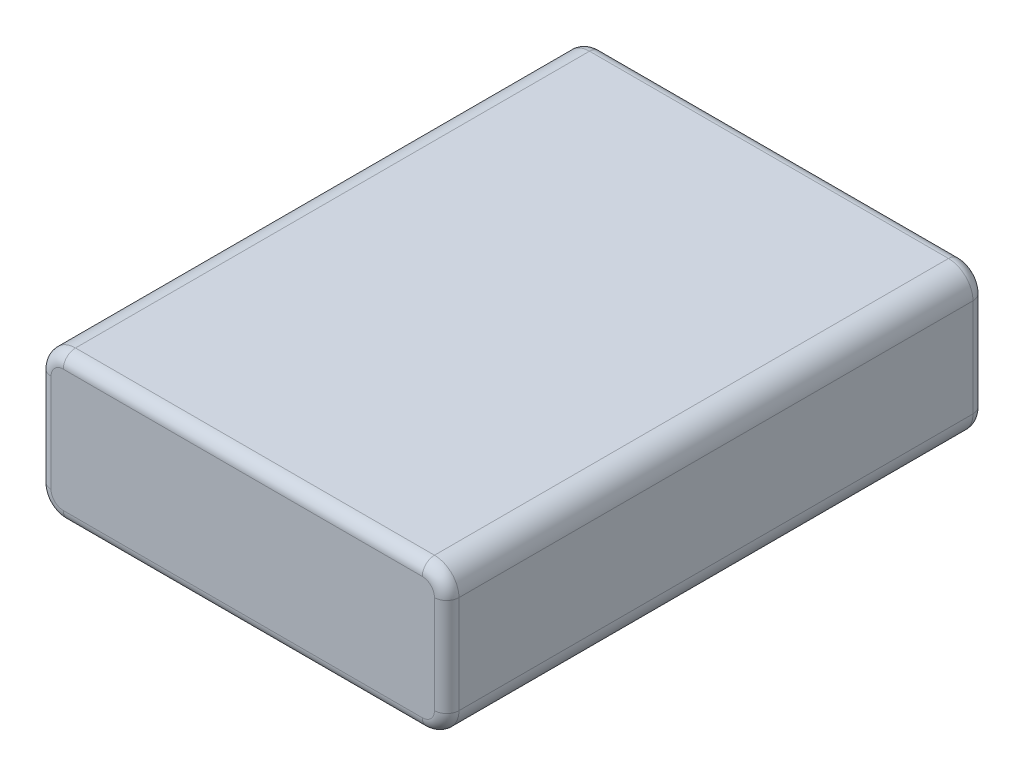
SolidWorks part; units mm, degrees
ref_plane "Front Plane" through (0, 0, 0) normal (0, 0, 1) x (1, 0, 0)
ref_plane "Top Plane" through (0, 0, 0) normal (0, 1, 0) x (1, 0, 0)
ref_plane "Right Plane" through (0, 0, 0) normal (1, 0, 0) x (0, 0, -1)
sketch "Sketch1" plane through (0, 0, 0) normal (0, 1, 0) x (1, 0, 0)
  line L1 (25, 0) -> (25, 33)
  line L2 (25, 33) -> (-25, 33)
  line L3 (-25, 33) -> (-25, -33)
  line L4 (-25, -33) -> (25, -33)
  line L5 (25, -33) -> (25, 0)
extrude "Boss-Extrude1" add sketch "Sketch1" along normal blind 18
fillet "Fillet1" radius 3 4 edges at (-25, 0, 0) (25, 0, 0) (-25, 18, 0) (25, 18, 0)
fillet "Fillet2" radius 1.5 16 edges at (-24.1213, 17.1213, -33) (-25, 9, -33) (-24.1213, 0.8787, -33) (0, 0, -33) (24.1213, 0.8787, -33) (25, 9, -33) (24.1213, 17.1213, -33) (0, 18, -33) (24.1213, 0.8787, 33) (0, 0, 33) (-24.1213, 0.8787, 33) (-25, 9, 33) (-24.1213, 17.1213, 33) (0, 18, 33) (24.1213, 17.1213, 33) (25, 9, 33)
